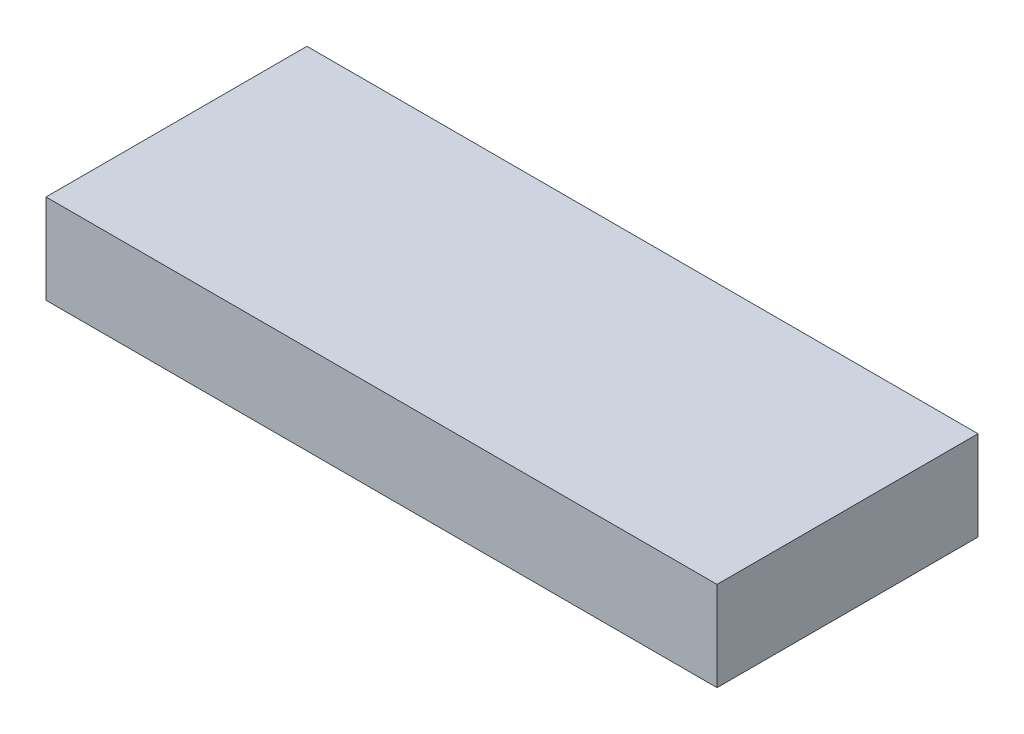
SolidWorks part; units mm, degrees
ref_plane "Front Plane" through (0, 0, 0) normal (0, 0, 1) x (1, 0, 0)
ref_plane "Top Plane" through (0, 0, 0) normal (0, 1, 0) x (1, 0, 0)
ref_plane "Right Plane" through (0, 0, 0) normal (1, 0, 0) x (0, 0, -1)
sketch "Sketch1" plane through (0, 0, 0) normal (0, 1, 0) x (1, 0, 0)
  line L1 (-134.4524, 68.432) -> (-44.4524, 68.432)
  line L2 (-134.4524, 68.432) -> (-134.4524, 33.432)
  line L3 (-134.4524, 33.432) -> (-44.4524, 33.432)
  line L4 (-44.4524, 68.432) -> (-44.4524, 33.432)
  line L5 (-134.4524, 68.432) -> (-44.4524, 33.432) construction
  line L6 (-134.4524, 33.432) -> (-44.4524, 68.432) construction
  point P0 (-89.4524, 50.932)
extrude "Command Strip Base" add sketch "Sketch1" along normal blind 12
